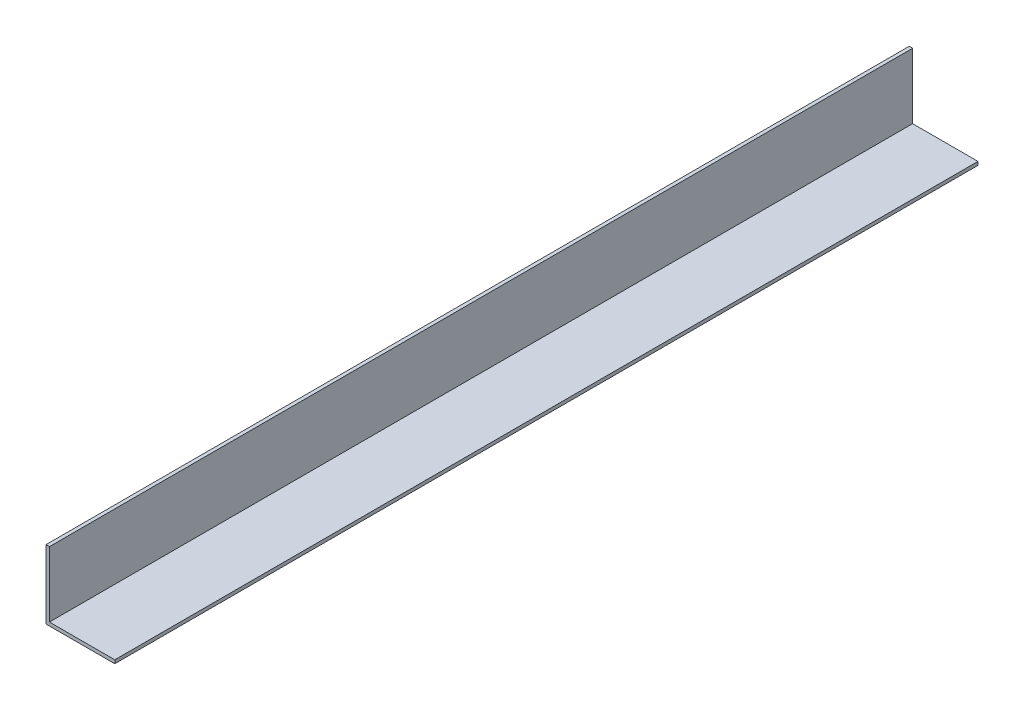
SolidWorks part; units mm, degrees
material "1060 Сплав"
ref_plane "Спереди" through (0, 0, 0) normal (0, 0, 1) x (1, 0, 0)
ref_plane "Сверху" through (0, 0, 0) normal (0, 1, 0) x (1, 0, 0)
ref_plane "Справа" through (0, 0, 0) normal (1, 0, 0) x (0, 0, -1)
sketch "Эскиз1" plane through (0, 0, 0) normal (0, 0, 1) x (1, 0, 0)
  line L0 (0, 0) -> (0, 20)
  line L1 (0, 20) -> (1, 20)
  line L2 (1, 20) -> (1, 1)
  line L3 (1, 1) -> (20, 1)
  line L4 (20, 1) -> (20, 0)
  line L5 (20, 0) -> (0, 0)
  dimension "D1" = 20
  dimension "D2" = 1
extrude "Бобышка-Вытянуть1" add sketch "Эскиз1" along normal blind 251
